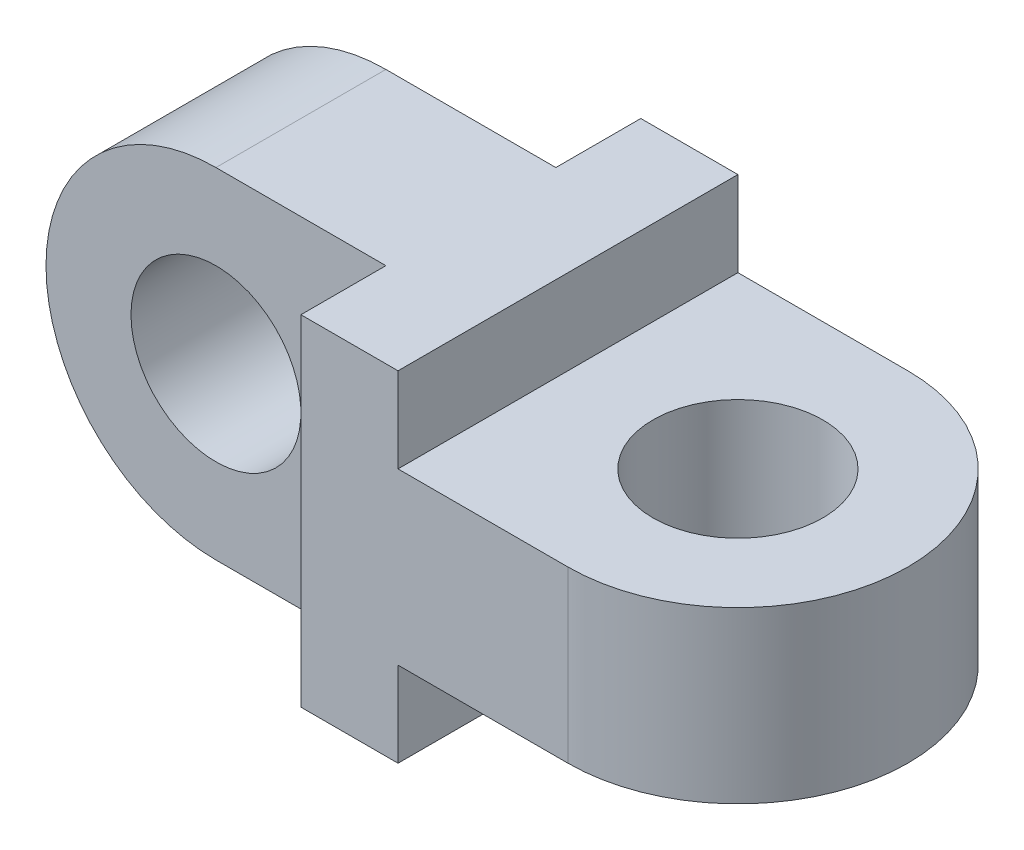
SolidWorks part; units mm, degrees
ref_plane "Front Plane" through (0, 0, 0) normal (0, 0, 1) x (1, 0, 0)
ref_plane "Top Plane" through (0, 0, 0) normal (0, 1, 0) x (1, 0, 0)
ref_plane "Right Plane" through (0, 0, 0) normal (1, 0, 0) x (0, 0, -1)
sketch "Sketch1" plane through (0, 0, 0) normal (0, 1, 0) x (1, 0, 0)
  line L0 (0, 14) -> (0, -14)
  line L1 (0, -14) -> (14, -14)
  line L2 (14, 14) -> (0, 14)
  line L3 (14, 14) -> (14, -14) construction
  arc A0 (14, -14) -> (14, 14) centre (14, 0) ccw
  circle A1 centre (14, 0) radius 7
  dimension "D1" = 14
  dimension "D2" = 14
  dimension "D3" = 14
extrude "Boss-Extrude1" add sketch "Sketch1" along normal mid plane 14
sketch "Sketch2" plane through (0, 0, 0) normal (-1, 0, 0) x (0, 0, 1)
  line L1 (-14, -14) -> (14, -14)
  line L2 (-14, -14) -> (-14, 14)
  line L3 (-14, 14) -> (14, 14)
  line L4 (14, -14) -> (14, 14)
  line L5 (-14, -14) -> (14, 14) construction
  line L6 (-14, 14) -> (14, -14) construction
  point P0 (0, 0)
  dimension "D1" = 28
extrude "Boss-Extrude2" add sketch "Sketch2" along normal blind 8
ref_plane "Plane1" through (0, 0, 0) normal (0, 0, -1) x (-1, 0, 0)
sketch "Sketch3" plane through (0, 0, 0) normal (0, 0, -1) x (-1, 0, 0)
  line L0 (8, 14) -> (8, -14) construction
  line L1 (8, 14) -> (8, -14)
  line L2 (8, 0) -> (22, 0) construction
  line L3 (8, 14) -> (22, 14)
  line L4 (22, -14) -> (8, -14)
  circle A0 centre (22, 0) radius 7
  arc A1 (22, 14) -> (22, -14) centre (22, 0) cw
  point P9 (0, 0)
  dimension "D1" = 14
  dimension "D2" = 14
extrude "Boss-Extrude3" add sketch "Sketch3" along normal mid plane 14
